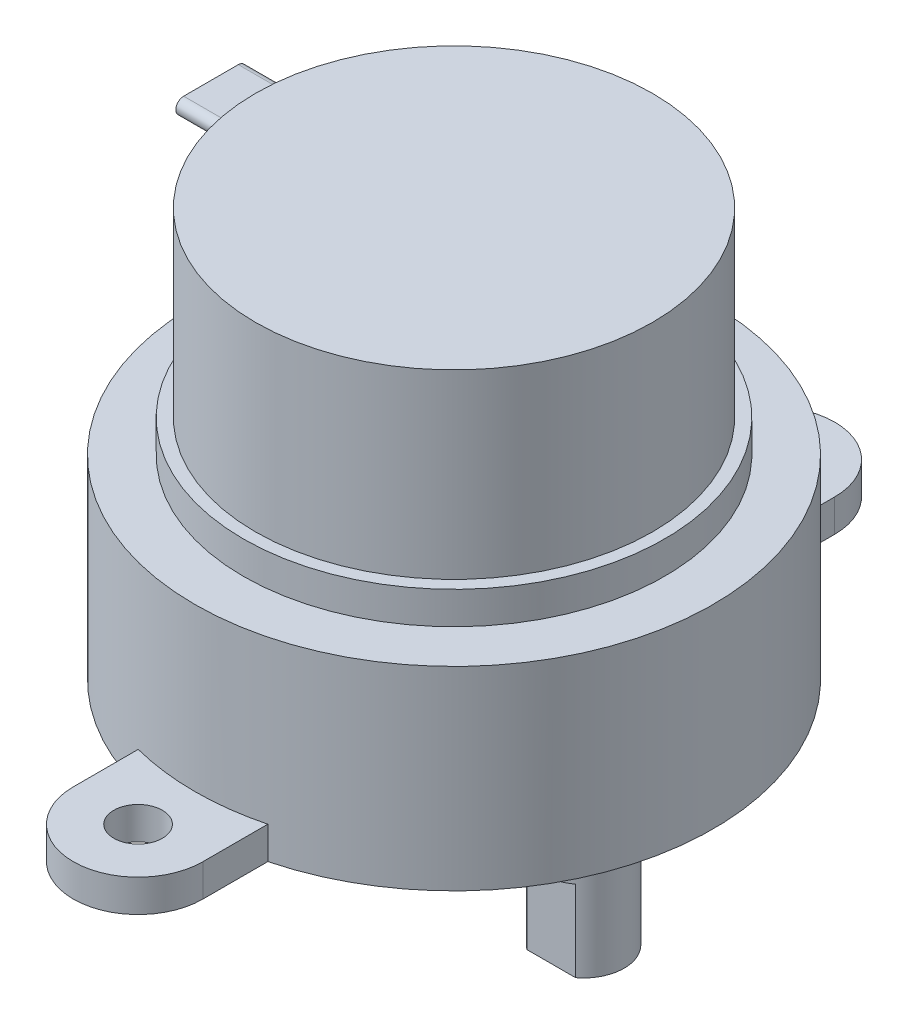
SolidWorks part; units mm, degrees
ref_plane "前视基准面" through (0, 0, 0) normal (0, 0, 1) x (1, 0, 0)
ref_plane "上视基准面" through (0, 0, 0) normal (0, 1, 0) x (1, 0, 0)
ref_plane "右视基准面" through (0, 0, 0) normal (1, 0, 0) x (0, 0, -1)
other "Configuration Table"
sketch "草图1" plane through (0, 0, 0) normal (0, 0, 1) x (1, 0, 0)
  line L0 (0, 0) -> (-16, 0)
  line L1 (-16, 0) -> (-16, 12)
  line L2 (-16, 12) -> (-13, 12)
  line L3 (-13, 12) -> (-13, 14)
  line L4 (-13, 14) -> (-12.25, 14)
  line L5 (-12.25, 14) -> (-12.25, 25.2)
  line L6 (-12.25, 25.2) -> (0, 25.2)
  line L7 (0, 25.2) -> (0, 0) construction
  line L8 (0, 0) -> (0, 25.2)
  dimension "D1" = 32
  dimension "D2" = 12
  dimension "D3" = 26
  dimension "D4" = 24.5
  dimension "D5" = 2
  dimension "D6" = 25.2
revolve "旋转1" add sketch "草图1" angle 360 about L7
sketch "草图2" plane through (0, 0, 0) normal (0, 0, 1) x (1, 0, 0)
  line L0 (8, 0) -> (8, -10.2) construction
  line L1 (-16, 0) -> (16, 0) construction
  line L2 (8, -10.2) -> (5.5, -10.2)
  line L3 (5.5, -10.2) -> (5.5, -2.7)
  line L4 (5.5, -2.7) -> (4, -2.7)
  line L5 (4, -2.7) -> (4, -1.25)
  line L6 (4, -1.25) -> (3.5, -1.25)
  line L7 (3.5, -1.25) -> (3.5, 0)
  line L8 (3.5, 0) -> (8, 0)
  line L9 (8, 0) -> (8, -10.2)
  dimension "D1" = 5
  dimension "D2" = 8
  dimension "D3" = 8
  dimension "D4" = 1.25
  dimension "D5" = 2.7
  dimension "D6" = 9
  dimension "D7" = 10.2
revolve "旋转2" add sketch "草图2" angle 360 about L0
hole_wizard "M4 螺纹孔1" positions "草图3" profile "草图4" tap size "M4" standard "GB"
sketch "草图3" plane through (0, -10.2, 0) normal (0, -1, 0) x (-1, 0, 0)
  point P0 (-8, 0)
cosmetic thread "孔螺蚊线1" parameters "D1"=6, "D2"=4
sketch "草图4" plane through (8, -10.2, 0) normal (1, 0, 0) x (0, 0, -1)
  line L0 (0, 0) -> (0, 8.4914)
  line L1 (0, 8.4914) -> (1.65, 7.5)
  line L2 (1.65, 7.5) -> (1.65, 0)
  line L5 (1.65, 0) -> (0, 0)
  line L10 (0, 8.4914) -> (-1.65, 7.5) construction
  line L11 (0, -6.35) -> (0, 107.95) construction
  dimension "螺纹孔钻头直径" = 3.3
  dimension "螺纹孔钻头深度" = 7.5
  dimension "导头角度" = 118
sketch "草图5" plane through (0, 0, 0) normal (0, -1, 0) x (1, 0, 0)
  line L0 (8, 0) -> (19.9064, 0) construction
  line L2 (12.7459, 2) -> (2.4257, 2)
  line L3 (12.7459, 2) -> (12.7459, 5.57)
  line L4 (12.7459, 5.57) -> (2.4257, 5.57)
  line L5 (2.4257, 2) -> (2.4257, 5.57)
  line L6 (12.7459, -4.5031) -> (0.9279, -4.5031)
  line L7 (12.7459, -4.5031) -> (12.7459, -2)
  line L8 (12.7459, -2) -> (0.9279, -2)
  line L9 (0.9279, -4.5031) -> (0.9279, -2)
  dimension "D1" = 4
extrude "切除-拉伸1" cut sketch "草图5" against normal blind 5 from surface at 10.2 contours L3 L4 L5 L2 | L7 L8 L9 L6 starting at face at (8, -10.2, -1.65)
sketch "草图6" plane through (0, 0, 0) normal (0, -1, 0) x (1, 0, 0)
  line L0 (0, 19.5) -> (0, -19.5) construction
  line L1 (4, 19.5) -> (4, -19.5)
  line L2 (-4, 19.5) -> (-4, -19.5)
  arc A0 (4, 19.5) -> (-4, 19.5) centre (0, 19.5) ccw
  arc A1 (-4, -19.5) -> (4, -19.5) centre (0, -19.5) ccw
  circle A2 centre (0, -19.5) radius 1.5
  circle A3 centre (0, 19.5) radius 1.5
  point P2 (0, 0)
  dimension "D2" = 8
  dimension "D3" = 3
  dimension "D1" = 39
extrude "凸台-拉伸1" add sketch "草图6" against normal blind 2
sketch "草图7" plane through (0, 0, 0) normal (1, 0, 0) x (0, 0, -1)
  line L0 (0, 25.2) -> (0, 24.032)
  line L1 (12.25, 25.2) -> (-12.25, 25.2) construction
  line L2 (-1.6874, 24.032) -> (1.6874, 24.032) construction
  line L3 (-1.6874, 24.514) -> (1.6874, 24.514)
  line L4 (-1.6874, 23.5501) -> (1.6874, 23.5501)
  arc A0 (-1.6874, 24.514) -> (-1.6874, 23.5501) centre (-1.6874, 24.032) ccw
  arc A1 (1.6874, 23.5501) -> (1.6874, 24.514) centre (1.6874, 24.032) ccw
  point P7 (0, 24.032)
extrude "凸台-拉伸2" add sketch "草图7" against normal blind 15 contours L4 A1 L3 A0
